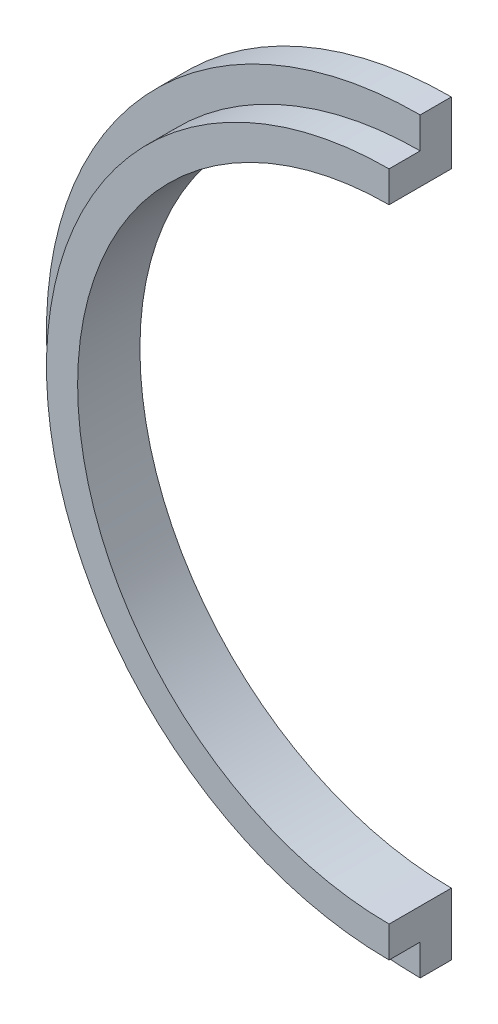
SolidWorks part; units mm, degrees
material "6061-T6 (SS)"
ref_plane "Alzado" through (0, 0, 0) normal (0, 0, 1) x (1, 0, 0)
ref_plane "Planta" through (0, 0, 0) normal (0, 1, 0) x (1, 0, 0)
ref_plane "Vista lateral" through (0, 0, 0) normal (1, 0, 0) x (0, 0, -1)
sketch "Sketch1" plane through (0, 0, 0) normal (0, 0, 1) x (1, 0, 0)
  circle A0 centre (0, 0) radius 180
  circle A1 centre (0, 0) radius 150
  dimension "D1" = 360
  dimension "D2" = 30
extrude "Boss-Extrude1" add sketch "Sketch1" along normal blind 15 contours A1
sketch "Sketch2" plane through (0, 0, 15) normal (0, 0, 1) x (1, 0, 0)
  circle A0 centre (0, 0) radius 150
  circle A1 centre (0, 0) radius 165
  circle A2 centre (0, 0) radius 150 construction
  point P4 (0, 0)
  dimension "D1" = 15
extrude "Boss-Extrude2" add sketch "Sketch2" along normal blind 15
sketch "Sketch3" plane through (0, 0, 0) normal (0, 0, 1) x (1, 0, 0)
  line L0 (0, 180) -> (0, -180)
  line L1 (0, -180) -> (245, -180)
  line L2 (245, -180) -> (245, 180)
  line L3 (245, 180) -> (0, 180)
  circle A0 centre (0, 0) radius 180 construction
  dimension "D1" = 245
extrude "Cut-Extrude1" cut sketch "Sketch3" along normal up to next
